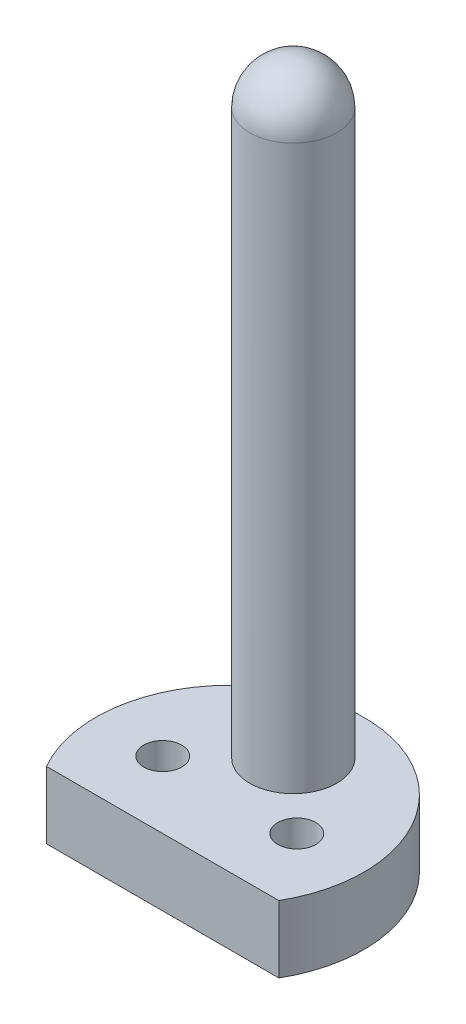
SolidWorks part; units mm, degrees
ref_plane "Front Plane" through (0, 0, 0) normal (0, 0, 1) x (1, 0, 0)
ref_plane "Top Plane" through (0, 0, 0) normal (0, 1, 0) x (1, 0, 0)
ref_plane "Right Plane" through (0, 0, 0) normal (1, 0, 0) x (0, 0, -1)
sketch "Sketch1" plane through (0, 0, 0) normal (0, 1, 0) x (1, 0, 0)
  line L0 (-8.6603, -5) -> (8.6603, -5)
  arc A0 (8.6603, -5) -> (-8.6603, -5) centre (0, 0) ccw
  circle A1 centre (-5, 0) radius 1.42
  circle A2 centre (5, 0) radius 1.42
  dimension "D3" = 20
  dimension "D4" = 5
  dimension "D5" = 2.84
  dimension "D6" = 2.84
  dimension "D1" = 5
  dimension "D2" = 5
extrude "Boss-Extrude1" add sketch "Sketch1" along normal blind 5
sketch "Sketch3" plane through (0, 5, 0) normal (0, 1, 0) x (1, 0, 0)
  circle A0 centre (0, 4.7348) radius 3.25
  dimension "D1" = 6.5
extrude "Boss-Extrude2" add sketch "Sketch3" along normal blind 42
sketch "Sketch6" plane through (0, 47, 0) normal (0, 1, 0) x (1, 0, 0)
  line L0 (0, 7.9848) -> (0, 0) construction
  circle A0 centre (0, 4.7348) radius 3.25 construction
  circle A1 centre (0, 4.7348) radius 3.25 construction
revolve "Revolve1" add sketch "Sketch6" angle 360 about L0
